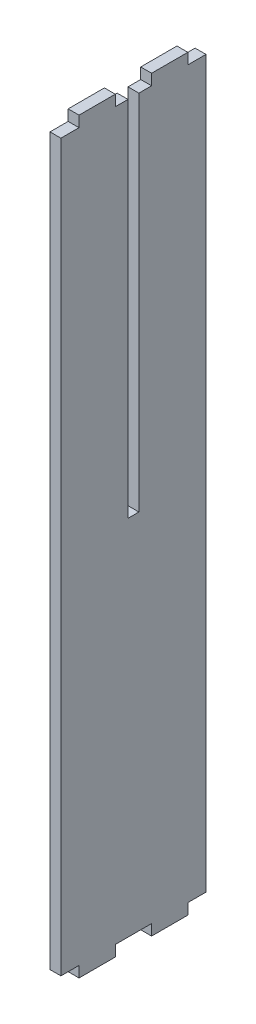
SolidWorks part; units mm, degrees
material "Balsa"
ref_plane "Alzado" through (0, 0, 0) normal (0, 0, 1) x (1, 0, 0)
ref_plane "Planta" through (0, 0, 0) normal (0, 1, 0) x (1, 0, 0)
ref_plane "Vista lateral" through (0, 0, 0) normal (1, 0, 0) x (0, 0, -1)
sketch "Croquis1" plane through (0, 0, 0) normal (1, 0, 0) x (0, 0, -1)
  line L0 (-20, 0) -> (-15, 0)
  line L1 (20, 0) -> (20, 200)
  line L2 (20, 200) -> (15, 200)
  line L3 (15, 200) -> (15, 203)
  line L4 (15, 203) -> (5, 203)
  line L5 (-20, 0) -> (-20, 200)
  line L6 (-20, 200) -> (-15, 200)
  line L7 (-15, 200) -> (-15, 203)
  line L8 (-15, 203) -> (-5, 203)
  line L9 (-5, 203) -> (-5, 200)
  line L10 (-5, 200) -> (5, 200)
  line L11 (5, 200) -> (5, 203)
  line L12 (-15, 0) -> (-15, -3)
  line L13 (-15, -3) -> (-5, -3)
  line L14 (-5, -3) -> (-5, 0)
  line L15 (5, 0) -> (5, -3)
  line L16 (5, -3) -> (15, -3)
  line L17 (15, -3) -> (15, 0)
  line L18 (-5, 0) -> (5, 0)
  line L19 (15, 0) -> (20, 0)
  point P3 (0, 0)
  dimension "D1" = 40
  dimension "D3" = 10
  dimension "D4" = 3
  dimension "D5" = 200
extrude "Saliente-Extruir1" add sketch "Croquis1" along normal mid plane 3
sketch "Croquis2" plane through (1.5, 0, 0) normal (1, 0, 0) x (0, 0, -1)
  line L0 (5, 200) -> (-5, 200) construction
  line L5 (-1.5, 200) -> (1.5, 200)
  line L6 (-1.5, 200) -> (-1.5, 100)
  line L7 (-1.5, 100) -> (1.5, 100)
  line L8 (1.5, 200) -> (1.5, 100)
  point P8 (0, 200)
  dimension "D1" = 3
  dimension "D2" = 100
extrude "Cortar-Extruir1" cut sketch "Croquis2" against normal up to next
sketch "Croquis3" [suppressed] plane through (1.5, 0, 0) normal (1, 0, 0) x (0, 0, -1)
  line L0 (-20, 0) -> (-15, 0) construction
  line L1 (-1.5, 0) -> (1.5, 0)
  line L2 (-1.5, 0) -> (-1.5, 100)
  line L3 (-1.5, 100) -> (1.5, 100)
  line L4 (1.5, 0) -> (1.5, 100)
  dimension "D1" = 100
  dimension "D2" = 3
extrude "Cortar-Extruir2" [suppressed] cut sketch "Croquis3" against normal up to next
equation "\"r\"= 20"
equation "\"D1@Croquis1\"=\"r\"*2"
equation "\"D2@Croquis1\"=\"r\"/2"
equation "\"D3@Croquis1\"=\"r\"/2"
equation "\"g\"= 3"
equation "\"D4@Croquis1\"=\"g\""
equation "\"D1@Saliente-Extruir1\"=\"g\""
equation "\"L\"= 200"
equation "\"D5@Croquis1\"=\"L\""
equation "\"D1@Croquis3\"=\"L\"/2"
equation "\"D2@Croquis3\"=\"g\""
equation "\"D1@Croquis2\"=\"g\""
equation "\"D2@Croquis2\"=\"L\"/2"
